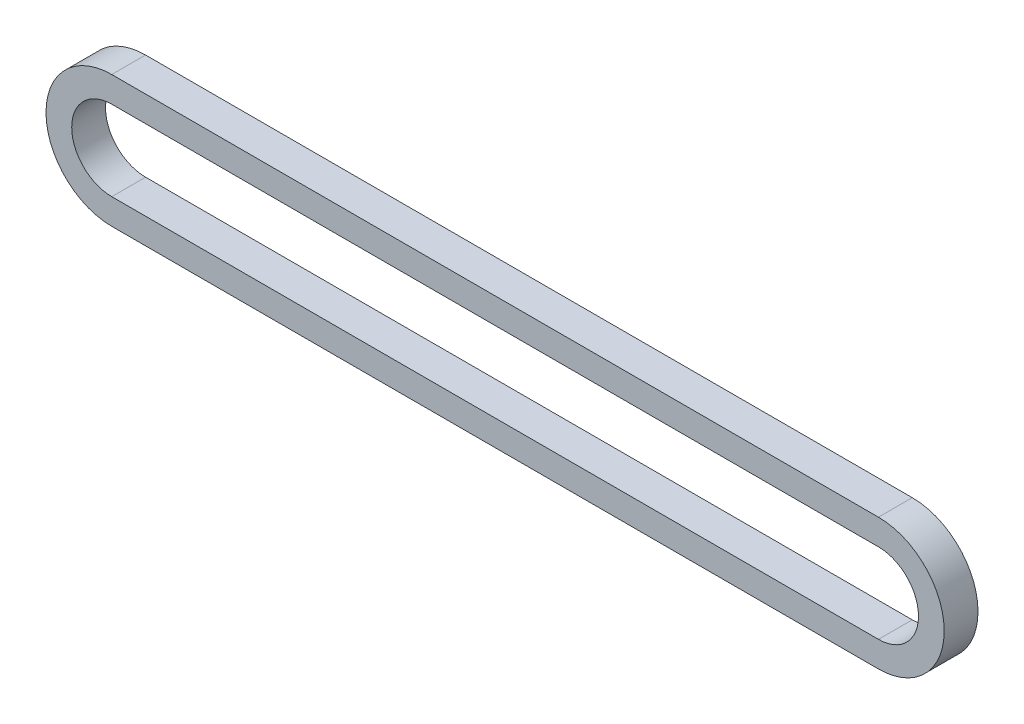
SolidWorks part; units mm, degrees
ref_plane "Front Plane" through (0, 0, 0) normal (0, 0, 1) x (1, 0, 0)
ref_plane "Top Plane" through (0, 0, 0) normal (0, 1, 0) x (1, 0, 0)
ref_plane "Right Plane" through (0, 0, 0) normal (1, 0, 0) x (0, 0, -1)
sketch "Sketch1" plane through (0, 0, 0) normal (0, 0, 1) x (1, 0, 0)
  line L0 (0, 18.4009) -> (266.7, 18.4009)
  line L1 (0, -18.4009) -> (266.7, -18.4009)
  line L2 (0, 0) -> (266.7, 0) construction
  arc A0 (0, 18.4009) -> (0, -18.4009) centre (0, 0) ccw
  arc A1 (266.7, -18.4009) -> (266.7, 18.4009) centre (266.7, 0) ccw
  dimension "D2" = 36.8018
  dimension "D3" = 36.8018
  dimension "D1" = 266.7
extrude "Extrude-Thin1" add sketch "Sketch1" along normal mid plane 11.7602 thin thin type mid plane wall 8.9408
equation "\"Center Distance\"= 10.5"
equation "\"D1@Sketch1\"=\"Center Distance\""
equation "\"Pitch\"= 0.375"
equation "\"T1\"= 12"
equation "\"T2\"= 12"
equation "\"D2@Sketch1\"=\"Pitch\"/(sin( 180/\"T1\"))"
equation "\"D3@Sketch1\"=\"Pitch\"/(sin( 180/\"T2\"))"
equation "\"Links\"= 2 * \"Center Distance\" / \"Pitch\" + ( \"T1\" + \"T2\" ) / 2 + ( ( \"T2\" - \"T1\" ) / ( 2 * 3.14159 ) ) ^ 2 * \"Pitch\" / \"Center Distance\""
